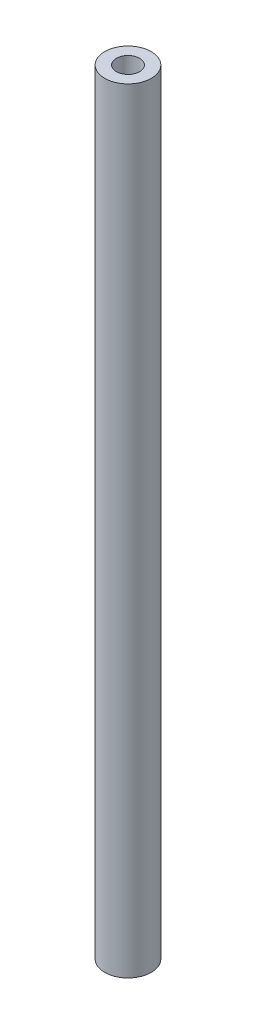
SolidWorks part; units mm, degrees
ref_plane "前视基准面" through (0, 0, 0) normal (0, 0, 1) x (1, 0, 0)
ref_plane "上视基准面" through (0, 0, 0) normal (0, 1, 0) x (1, 0, 0)
ref_plane "右视基准面" through (0, 0, 0) normal (1, 0, 0) x (0, 0, -1)
sketch "草图1" plane through (0, 0, 0) normal (0, 1, 0) x (1, 0, 0)
  circle A0 centre (0, 0) radius 3
  circle A1 centre (0, 0) radius 1.5
  dimension "D1" = 6
  dimension "D2" = 3
extrude "凸台-拉伸1" add sketch "草图1" along normal blind 100
